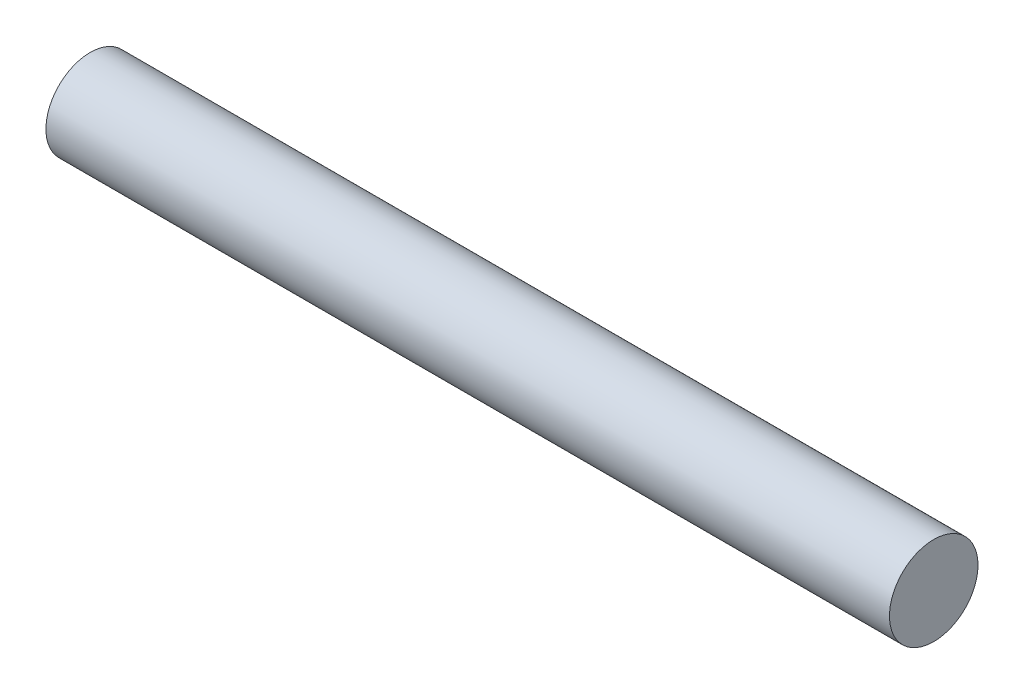
SolidWorks part; units mm, degrees
material "6061 Alloy"
ref_plane "Front Plane" through (0, 0, 0) normal (0, 0, 1) x (1, 0, 0)
ref_plane "Top Plane" through (0, 0, 0) normal (0, 1, 0) x (1, 0, 0)
ref_plane "Right Plane" through (0, 0, 0) normal (1, 0, 0) x (0, 0, -1)
sketch "Sketch1" plane through (0, 0, 0) normal (1, 0, 0) x (0, 0, -1)
  circle A0 centre (0, 0) radius 1.5875
  dimension "D1" = 3.175
extrude "Boss-Extrude1" add sketch "Sketch1" along normal mid plane 30.2543 contours A0
